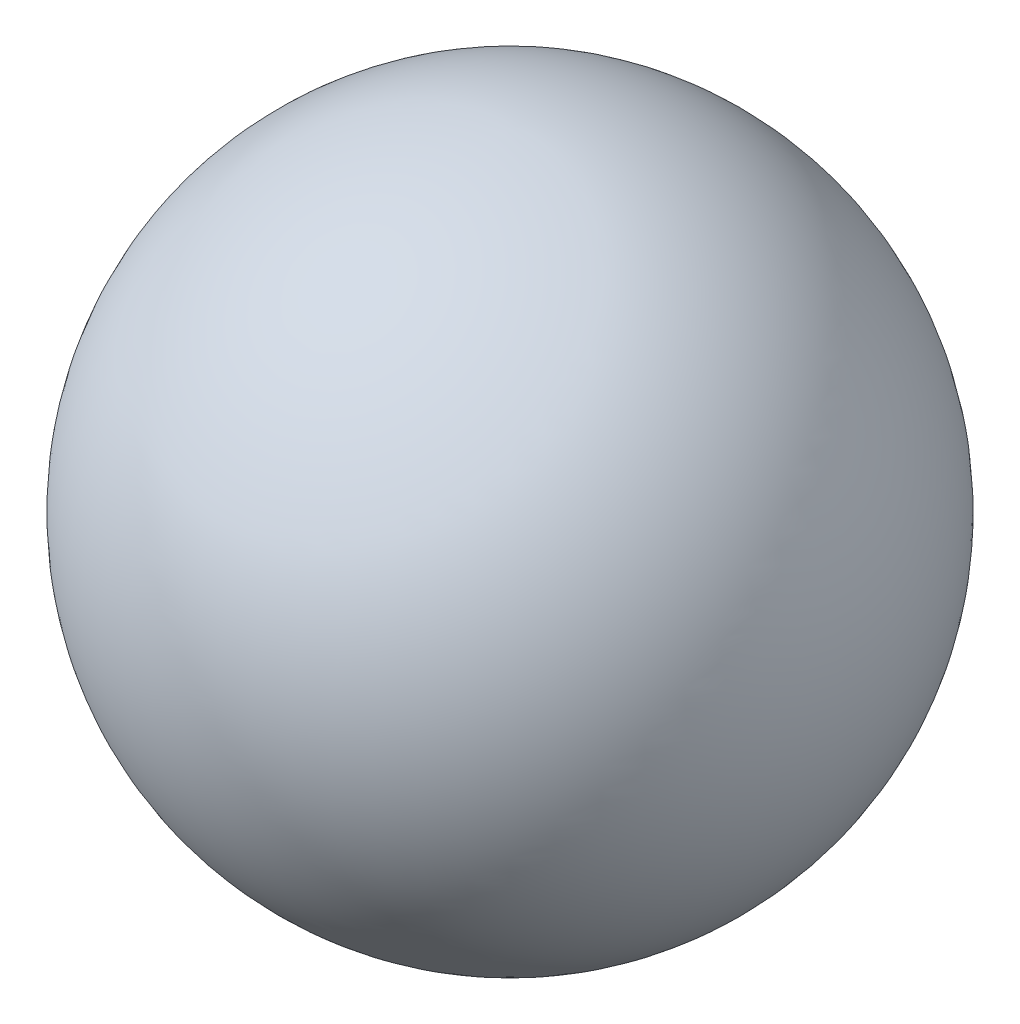
SolidWorks part; units mm, degrees
material "ASTM A36 Steel"
ref_plane "Front Plane" through (0, 0, 0) normal (0, 0, 1) x (1, 0, 0)
ref_plane "Top Plane" through (0, 0, 0) normal (0, 1, 0) x (1, 0, 0)
ref_plane "Right Plane" through (0, 0, 0) normal (1, 0, 0) x (0, 0, -1)
sketch "Sketch1" plane through (0, 0, 0) normal (0, 0, 1) x (1, 0, 0)
  line L0 (0, 6.35) -> (0, -6.35) construction
  line L1 (0, 6.35) -> (0, -6.35)
  arc A0 (0, 6.35) -> (0, -6.35) centre (-0.0892, 0) cw
  point P2 (0, 0)
  dimension "D1" = 12.7
revolve "Revolve1" add sketch "Sketch1" angle 360 about L0
